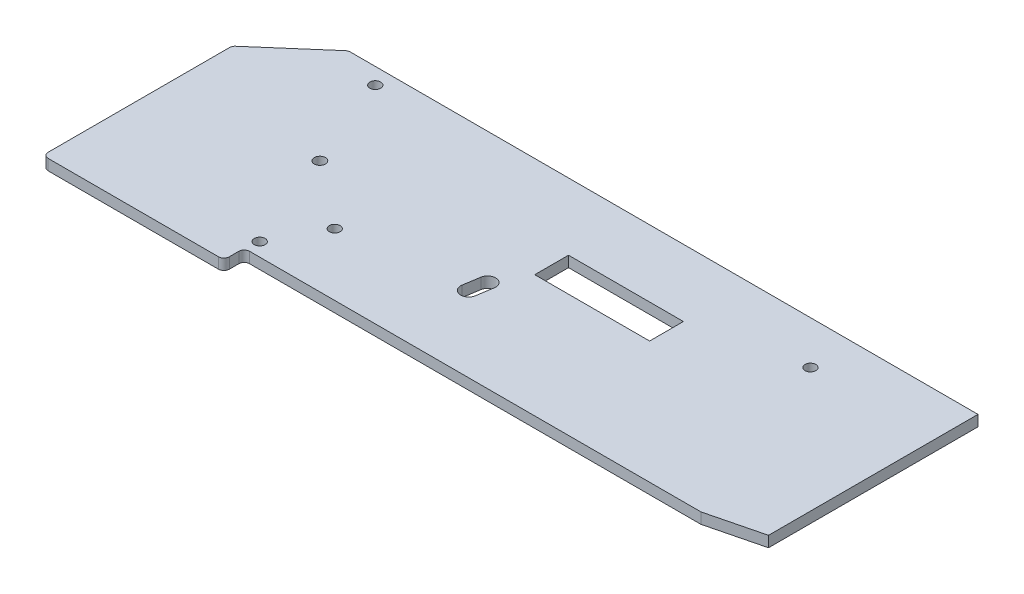
SolidWorks part; units mm, degrees
ref_plane "Front Plane" through (0, 0, 0) normal (0, 0, 1) x (1, 0, 0)
ref_plane "Top Plane" through (0, 0, 0) normal (0, 1, 0) x (1, 0, 0)
ref_plane "Right Plane" through (0, 0, 0) normal (1, 0, 0) x (0, 0, -1)
sketch "Sketch1" plane through (0, 0, 0) normal (0, 1, 0) x (1, 0, 0)
  line L0 (0, 0) -> (-23, -20)
  line L1 (-23, -20) -> (-23, -90)
  line L2 (0, 0) -> (233, 0)
  line L3 (233, 0) -> (233, -77.5)
  line L4 (44, -90) -> (-23, -90)
  line L7 (213, -82.5) -> (44, -82.5)
  line L8 (44, -82.5) -> (44, -90)
  line L10 (213, -82.5) -> (233, -77.5)
  circle A1 centre (16, -6) radius 2
  circle A2 centre (30, -40.5) radius 2.075
  circle A3 centre (54.5, -59.5) radius 2
  circle A4 centre (44.75, -77.5) radius 2
  circle A6 centre (187, -16) radius 2
  point P18 (187, -16)
  point P22 (44.75, -77.5)
  dimension "D1" = 4
  dimension "D4" = 4.15
  dimension "D7" = 4
  dimension "D10" = 4
  dimension "D15" = 4
  dimension "D23" = 20
  dimension "D2" = 16
  dimension "D3" = 6
  dimension "D5" = 34.5
  dimension "D6" = 14
  dimension "D8" = 24.5
  dimension "D9" = 19
  dimension "D11" = 18
  dimension "D12" = 14.75
  dimension "D16" = 43.5
  dimension "D17" = 132.5
  dimension "D18" = 256
  dimension "D19" = 67
  dimension "D20" = 20
  dimension "D21" = 90
  dimension "D22" = 23
  dimension "D24" = 5
  dimension "D25" = 7.5
extrude "Primary" add sketch "Sketch1" along normal blind 4
sketch "Sketch7" plane through (0, 4, 0) normal (0, 1, 0) x (1, 0, 0)
  circle A1 centre (187, -16) radius 2
  circle A2 centre (187, -16) radius 7.5
  point P1 (187, -16)
  dimension "D1" = 4
  dimension "D2" = 15
extrude "Swingybit_Pin Ext" add sketch "Sketch7" against normal blind 6 from surface at -4 starting at face at (44.75, 0, 79.5)
sketch "Sketch8" plane through (0, 4, 0) normal (0, 1, 0) x (1, 0, 0)
  circle A0 centre (16, -6) radius 2
  circle A1 centre (16, -6) radius 5
  circle A2 centre (54.5, -59.5) radius 8.75
  circle A3 centre (54.5, -59.5) radius 2
  circle A4 centre (54.5, -59.5) radius 2 construction
  point P0 (16, -6)
  point P5 (54.5, -59.5)
  dimension "D1" = 4
  dimension "D2" = 10
  dimension "D3" = 17.5
extrude "Wheel_Pin Ext" add sketch "Sketch8" against normal blind 1.75 from surface at -4 contours A1 | A0 | A2 | A3 starting at face at (54.5, 0, 61.5)
sketch "Sketch10" plane through (0, 4, 0) normal (0, 1, 0) x (1, 0, 0)
  line L1 (106.25, -37.25) -> (148.75, -37.25)
  line L2 (106.25, -37.25) -> (106.25, -24.75)
  line L3 (106.25, -24.75) -> (148.75, -24.75)
  line L4 (148.75, -37.25) -> (148.75, -24.75)
  line L5 (106.25, -37.25) -> (148.75, -24.75) construction
  line L6 (106.25, -24.75) -> (148.75, -37.25) construction
  line L8 (97.0814, -48.0315) -> (96.1328, -54.0315)
  line L9 (101.9496, -55.4255) -> (103.0446, -48.5)
  arc A0 (103.0446, -48.5) -> (97.0814, -48.0315) centre (100.0446, -48.5) ccw
  arc A1 (96.1328, -54.0315) -> (101.9496, -55.4255) centre (99.0959, -54.5) ccw
  point P0 (127.5, -31)
  point P20 (30, -40.5)
  dimension "D7" = 6
  dimension "D8" = 3
  dimension "D1" = 12.5
  dimension "D2" = 42.5
  dimension "D3" = 31
  dimension "D4" = 127.5
  dimension "D5" = 8
  dimension "D6" = 70.5
  dimension "D9" = 70.5
extrude "Window Cut" cut sketch "Sketch10" against normal through all
fillet "Fillet1" radius 2 5 edges at (0, 2, 0) (-23, 2, 20) (-23, 2, 90) (44, 2, 90) (44, 2, 82.5)
chamfer "Chamfer1" distance 0.5 angle 60 5 edges at (16, -1.75, 4) (30, 0, 42.575) (44.75, 0, 79.5) (54.5, -1.75, 57.5) (187, -6, 14)
